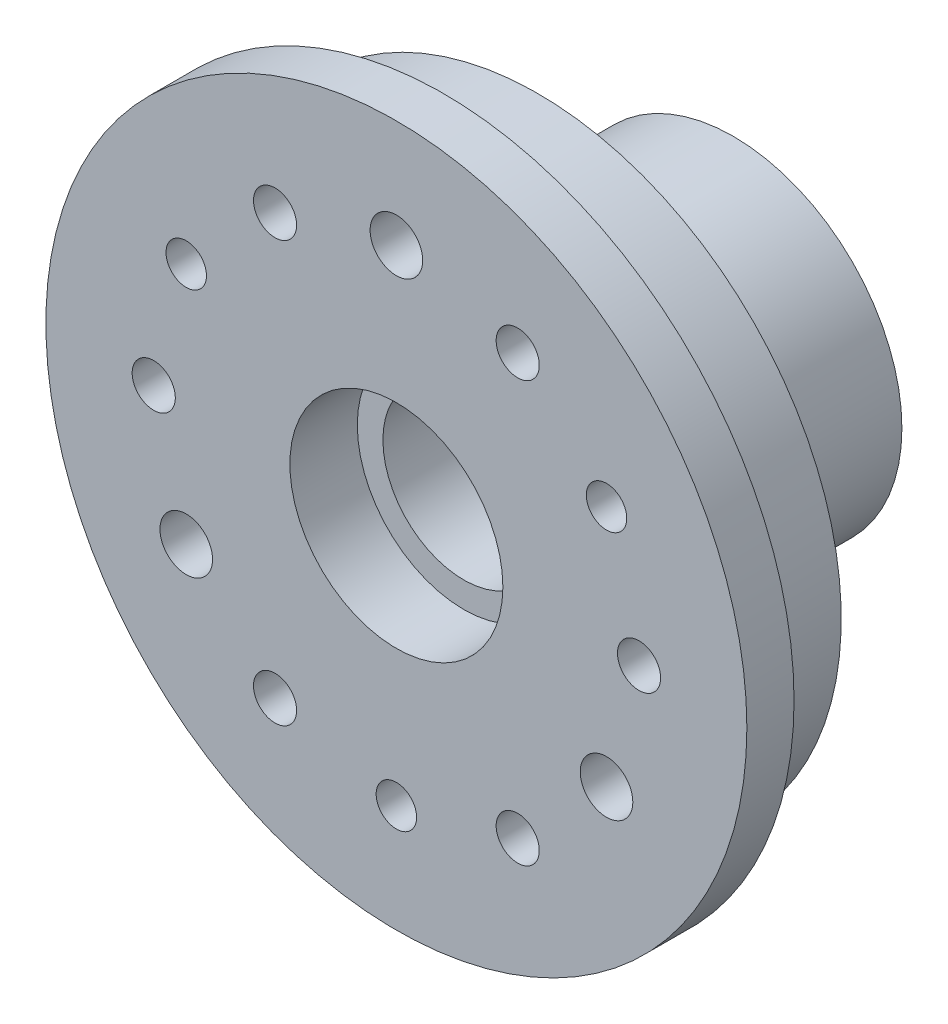
SolidWorks part; units mm, degrees
material "6061 Alloy"
ref_plane "Front Plane" through (0, 0, 0) normal (0, 0, 1) x (1, 0, 0)
ref_plane "Top Plane" through (0, 0, 0) normal (0, 1, 0) x (1, 0, 0)
ref_plane "Right Plane" through (0, 0, 0) normal (1, 0, 0) x (0, 0, -1)
sketch "Sketch1" plane through (0, 0, 0) normal (0, 0, 1) x (1, 0, 0)
  circle A7 centre (0, 0) radius 25
  point P17 (0, 0)
  dimension "D4" = 50
extrude "Boss-Extrude1" add sketch "Sketch1" along normal blind 20
sketch "Sketch2" plane through (0, 0, 20) normal (0, 0, 1) x (1, 0, 0)
  line L0 (0, 18) -> (0, 0) construction
  line L1 (0, 0) -> (-15.5885, -9) construction
  circle A0 centre (0, 0) radius 18 construction
  circle A1 centre (0, 18) radius 1.95
  circle A2 centre (15.5885, -9) radius 1.95
  circle A3 centre (-15.5885, -9) radius 1.95
  point P17 (0, 0)
  dimension "D1" = 36
  dimension "D2" = 3.9
  dimension "D3" = 3
extrude "Cut-Extrude1" cut sketch "Sketch2" against normal blind 4
sketch "Sketch4" plane through (0, 0, 20) normal (0, 0, 1) x (1, 0, 0)
  line L0 (0, 18) -> (0, 0) construction
  line L1 (0, 0) -> (15.5885, 9) construction
  circle A0 centre (0, 0) radius 18 construction
  circle A1 centre (15.5885, 9) radius 1.5
  circle A2 centre (0, -18) radius 1.5
  circle A3 centre (-15.5885, 9) radius 1.5
  point P18 (0, 0)
  dimension "D1" = 36
  dimension "D2" = 3
  dimension "D4" = 60
  dimension "D3" = 3
extrude "Cut-Extrude2" cut sketch "Sketch4" against normal through all
sketch "Sketch5" plane through (0, 0, 20) normal (0, 0, 1) x (1, 0, 0)
  circle A4 centre (0, 18) radius 2.45
  circle A5 centre (0, 18) radius 1.95 construction
  circle A6 centre (0, 18) radius 1.95
  dimension "D1" = 0.5
extrude "Boss-Extrude3" [suppressed] add sketch "Sketch5" along normal blind 1
fillet "Fillet1" [suppressed] radius 2
pattern_circular "CirPattern1" [suppressed] count 3 over 360
sketch "Sketch6" plane through (0, 0, 20) normal (0, 0, 1) x (1, 0, 0)
  circle A0 centre (0, 0) radius 7.9
  dimension "D1" = 15.8
extrude "Cut-Extrude3" cut sketch "Sketch6" against normal through all
ref_plane "Plane1" through (0, 0, 10) normal (0, 0, 1) x (1, 0, 0)
sketch "Sketch7" plane through (0, 0, 0) normal (0, 0, -1) x (-1, 0, 0)
  circle A0 centre (0, 0) radius 7.9
  circle A1 centre (0, 0) radius 7.9 construction
  circle A2 centre (0, 0) radius 6
  dimension "D1" = 12
extrude "Boss-Extrude4" add sketch "Sketch7" against normal blind 9 from offset 6 offset against normal yes
sketch "Sketch8" plane through (0, 0, 0) normal (0, 0, -1) x (-1, 0, 0)
  circle A0 centre (15.5885, 9) radius 1.5 construction
  circle A1 centre (0, -18) radius 1.5 construction
  circle A2 centre (0, 0) radius 7.9 construction
  circle A3 centre (-15.5885, 9) radius 1.5 construction
  circle A4 centre (0, 0) radius 25 construction
  circle A5 centre (15.5885, 9) radius 1.5
  circle A6 centre (0, -18) radius 1.5
  circle A7 centre (0, 0) radius 7.9
  circle A8 centre (-15.5885, 9) radius 1.5
  circle A9 centre (0, 0) radius 25
extrude "Boss-Extrude5" [suppressed] add sketch "Sketch8" along normal blind 1
sketch "Sketch9" plane through (0, 0, 20) normal (0, 0, 1) x (1, 0, 0)
  circle A0 centre (0, 0) radius 26
  circle A1 centre (0, 0) radius 25 construction
  circle A2 centre (0, 0) radius 25
  dimension "D1" = 1
extrude "Boss-Extrude6" add sketch "Sketch9" against normal blind 3.5
fillet "Fillet2" [suppressed] radius 0.5
fillet "Fillet3" [suppressed] radius 0.5
sketch "Sketch10" plane through (0, 0, 0) normal (0, 0, -1) x (-1, 0, 0)
  circle A0 centre (0, 0) radius 22.5
  circle A1 centre (0, 0) radius 25 construction
  circle A2 centre (0, 0) radius 25
  dimension "D1" = 45
extrude "Cut-Extrude5" cut sketch "Sketch10" against normal up to surface (16.5 mm away) up to face at (25, 0, 16.5)
sketch "Sketch11" plane through (0, 0, 0) normal (0, 0, -1) x (-1, 0, 0)
  circle A0 centre (0, 0) radius 22.5 construction
  circle A1 centre (0, 0) radius 22.5
  circle A2 centre (0, 0) radius 12.5
  dimension "D1" = 25
extrude "Cut-Extrude6" cut sketch "Sketch11" against normal blind 9.5
fillet "Fillet4" [suppressed] radius 1
fillet "Fillet5" [suppressed] radius 0.25
sketch "Sketch12" plane through (0, 0, 9.5) normal (0, 0, -1) x (-1, 0, 0)
  circle A0 centre (-15.5885, 9) radius 3
  dimension "D1" = 6
extrude "Cut-Extrude7" cut sketch "Sketch12" against normal blind 5
pattern_circular "CirPattern2" count 3 over 360 about axis through (0, 0, 0) along (0, 0, 1) of "Cut-Extrude7"
sketch "Sketch13" plane through (0, 0, 20) normal (0, 0, 1) x (1, 0, 0)
  line L0 (0, 18) -> (-9, 15.5885) construction
  line L1 (-9, 15.5885) -> (-15.5885, 9) construction
  circle A0 centre (0, 0) radius 18 construction
  circle A1 centre (-9, 15.5885) radius 1.6
  dimension "D1" = 36
  dimension "D2" = 3.2
extrude "Cut-Extrude8" cut sketch "Sketch13" against normal through all
pattern_circular "CirPattern3" count 6 over 360 about axis through (0, 0, 0) along (0, 0, 1) of "Cut-Extrude8"
sketch "Sketch14" plane through (0, 0, 20) normal (0, 0, 1) x (1, 0, 0)
  line L1 (-9, 11.547) -> (-5.5, 13.5677)
  line L2 (-5.5, 13.5677) -> (-5.5, 17.6092)
  line L3 (-5.5, 17.6092) -> (-9, 19.6299)
  line L4 (-9, 19.6299) -> (-12.5, 17.6092)
  line L5 (-12.5, 17.6092) -> (-12.5, 13.5677)
  line L6 (-12.5, 13.5677) -> (-9, 11.547)
  circle A0 centre (-9, 15.5885) radius 3.5 construction
  dimension "D1" = 7
extrude "Cut-Extrude9" [suppressed] cut sketch "Sketch14" against normal blind 5
pattern_circular "CirPattern4" [suppressed] count 6 over 360
sketch "Sketch15" plane through (0, 0, 0) normal (0, 0, -1) x (-1, 0, 0)
  circle A0 centre (0, 0) radius 7.9 construction
  circle A1 centre (0, 0) radius 12.5 construction
  circle A2 centre (0, 0) radius 7.9
  circle A3 centre (0, 0) radius 12.5
extrude "Boss-Extrude7" add sketch "Sketch15" along normal blind 5
